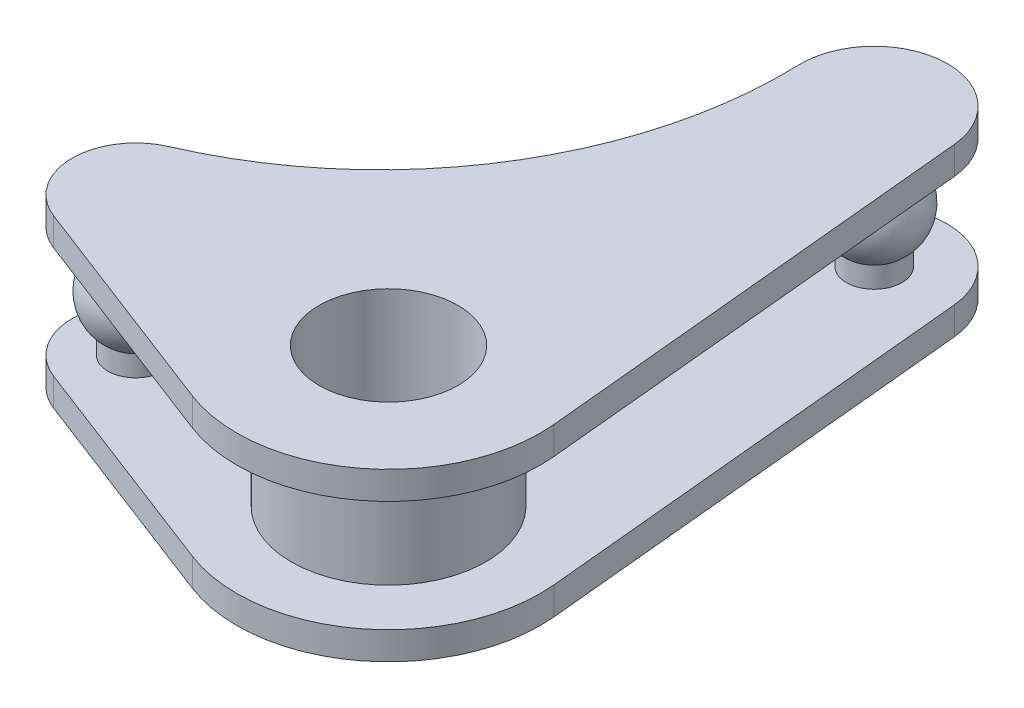
SolidWorks part; units mm, degrees
ref_plane "Front Plane" through (0, 0, 0) normal (0, 0, 1) x (1, 0, 0)
ref_plane "Top Plane" through (0, 0, 0) normal (0, 1, 0) x (1, 0, 0)
ref_plane "Right Plane" through (0, 0, 0) normal (1, 0, 0) x (0, 0, -1)
sketch "Sketch1" plane through (0, 0, 0) normal (0, 1, 0) x (1, 0, 0)
  line L0 (3.9168, 16.4489) -> (5.4393, 0.5199)
  line L1 (-10.0667, -1.9865) -> (-1.9593, -5.1007)
  line L2 (-9.2475, 0.1464) -> (0, 0) construction
  line L3 (0, 0) -> (1.2835, 16.1972) construction
  arc A0 (-10.1546, 2.2434) -> (-1.3604, 16.1119) centre (-15.9499, 15.6408) ccw
  arc A1 (-1.3604, 16.1119) -> (3.9168, 16.4489) centre (1.2835, 16.1972) cw
  arc A2 (-10.1546, 2.2434) -> (-10.0667, -1.9865) centre (-9.2475, 0.1464) ccw
  arc A3 (-1.9593, -5.1007) -> (5.4393, 0.5199) centre (0, 0) ccw
  circle A4 centre (0, 0) radius 2.5
  circle A5 centre (-9.2475, 0.1464) radius 0.0005
  circle A6 centre (1.2835, 16.1972) radius 0.0005
  dimension "D1" = 0.001
  dimension "D2" = 0.001
  dimension "D3" = 5
extrude "Boss-Extrude1" add sketch "Sketch1" along normal blind 6
shell "Shell2" thickness 1
sketch "Sketch3" plane through (0, 0, 0) normal (0, 1, 0) x (1, 0, 0)
  line L0 (3.9168, 16.4489) -> (5.4393, 0.5199)
  line L1 (-10.0667, -1.9865) -> (-1.9593, -5.1007)
  line L2 (-9.2475, 0.1464) -> (0, 0) construction
  line L3 (0, 0) -> (1.2835, 16.1972) construction
  arc A0 (-10.1546, 2.2434) -> (-1.3604, 16.1119) centre (-15.9499, 15.6408) ccw
  arc A1 (-1.3604, 16.1119) -> (3.9168, 16.4489) centre (1.2835, 16.1972) cw
  arc A2 (-10.1546, 2.2434) -> (-10.0667, -1.9865) centre (-9.2475, 0.1464) ccw
  arc A3 (-1.9593, -5.1007) -> (5.4393, 0.5199) centre (0, 0) ccw
  circle A4 centre (0, 0) radius 2.5
  circle A5 centre (-9.2475, 0.1464) radius 0.0005
  circle A6 centre (1.2835, 16.1972) radius 0.0005
  arc A7 (3.9168, 16.4489) -> (-1.3604, 16.1119) centre (1.2835, 16.1972) ccw construction
  arc A8 (-1.9593, -5.1007) -> (5.4393, 0.5199) centre (0, 0) ccw construction
  arc A9 (-10.1546, 2.2434) -> (-10.0667, -1.9865) centre (-9.2475, 0.1464) ccw construction
  arc A10 (-10.1546, 2.2434) -> (-1.3604, 16.1119) centre (-15.9499, 15.6408) ccw construction
  dimension "D1" = 0.001
  dimension "D2" = 0.001
  dimension "D3" = 5
sketch "Sketch4" plane through (0, 0, 0) normal (0, 0, 1) x (1, 0, 0)
  line L0 (0, 0) -> (0, 14.8904) construction
sketch3d "3DSketch3"
  line L0 (-9.2475, 0, -0.1464) -> (0, 0, 0) construction
  line L1 (0, 0, 0) -> (0, 14.8904, 0) construction
  line L2 (-9.2475, 0, -0.1464) -> (-9.248, 6, -0.1464) construction
  arc A0 (-9.2478, 4.6, -0.1464) -> (-9.2476, 1.4, -0.1464) centre (-9.2477, 3, -0.1464) ccw
  circle A1 centre (-9.2475, 6, -0.1464) radius 0.0005 construction
  point P9 (-9.273, 3, 1.4534)
  point P14 (-9.2475, 6.0005, -0.1464)
  dimension "D1" = 1.6
sketch "Sketch5" plane through (0, 0, 0) normal (-0.0158, 0, 0.9999) x (0.9999, 0, 0.0158)
  arc A0 (-9.249, 4.6) -> (-9.2491, 1.4) centre (-9.2489, 3) ccw
  arc A1 (-9.249, 4.6) -> (-9.2487, 1.4) centre (-9.2489, 3) ccw construction
sketch3d "3DSketch4"
  line L0 (0, 0, 0) -> (1.2835, 0, -16.1972) construction
  line L1 (0, 0, 0) -> (0, 14.8904, 0) construction
  line L2 (1.2835, 0, -16.1972) -> (1.2835, 6, -16.1977) construction
  circle A0 centre (1.2835, 6, -16.1972) radius 0.0005 construction
  point P10 (1.2835, 6.0005, -16.1972)
sketch "Sketch6" plane through (0, 0, 0) normal (0.9969, 0, 0.079) x (0.079, 0, -0.9969)
  line L0 (16.248, 0) -> (16.2485, 6) construction
  line L1 (16.2484, 4.6) -> (16.2481, 1.4)
  arc A0 (16.2484, 4.6) -> (16.2481, 1.4) centre (16.2483, 3) ccw
  dimension "D1" = 1.6
revolve "Revolve4" add sketch "Sketch6" angle 360 about L2
revolve "Revolve-Thin1" add sketch "Sketch5" angle 360 about L2 wall 1
